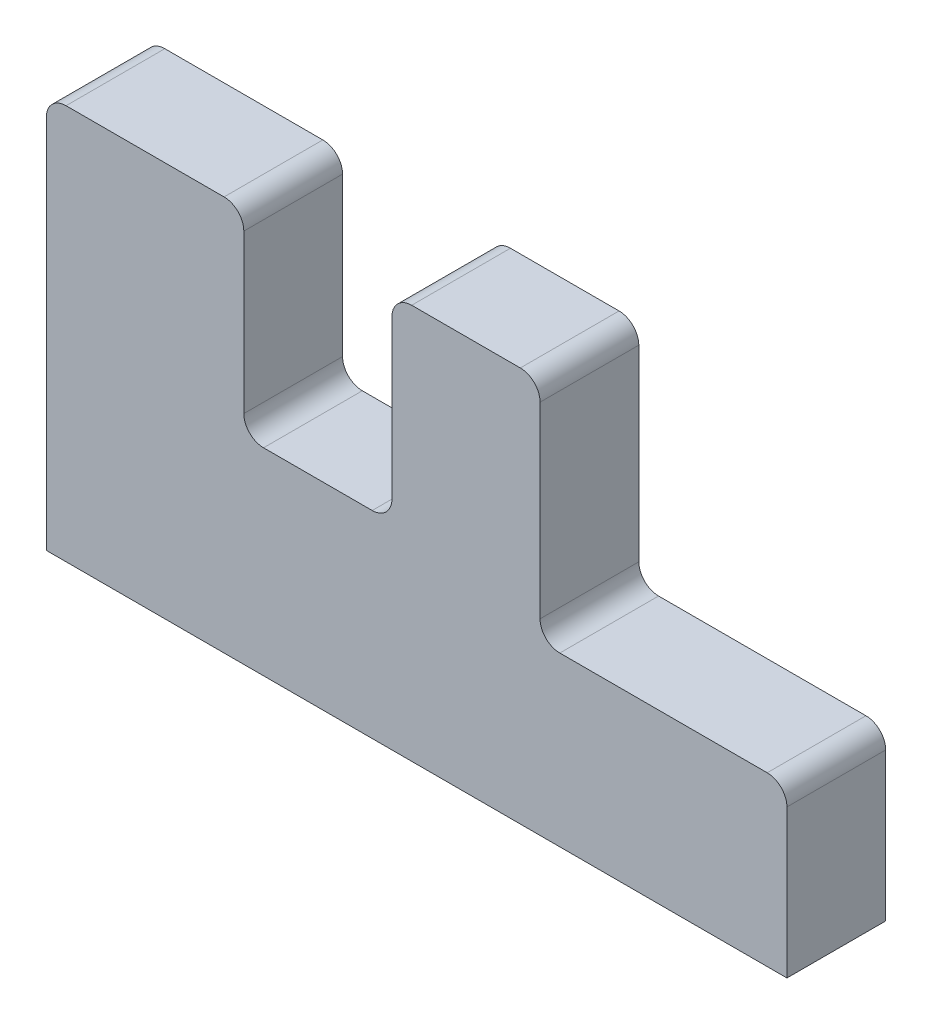
SolidWorks part; units mm, degrees
ref_plane "Front Plane" through (0, 0, 0) normal (0, 0, 1) x (1, 0, 0)
ref_plane "Top Plane" through (0, 0, 0) normal (0, 1, 0) x (1, 0, 0)
ref_plane "Right Plane" through (0, 0, 0) normal (1, 0, 0) x (0, 0, -1)
sketch "Sketch1" plane through (0, 0, 0) normal (0, 0, 1) x (1, 0, 0)
  line L0 (0, 0) -> (0, 50.8)
  line L1 (0, 50.8) -> (25.4, 50.8)
  line L2 (25.4, 50.8) -> (25.4, 25.4)
  line L3 (25.4, 25.4) -> (44.45, 25.4)
  line L4 (44.45, 25.4) -> (44.45, 50.8)
  line L5 (44.45, 50.8) -> (63.5, 50.8)
  line L6 (63.5, 50.8) -> (63.5, 21.59)
  line L7 (63.5, 21.59) -> (95.25, 21.59)
  line L8 (95.25, 21.59) -> (95.25, 0)
  line L9 (95.25, 0) -> (0, 0)
  point P13 (-55.7169, 45.0924)
  dimension "D1" = 95.25
  dimension "D2" = 50.8
  dimension "D3" = 25.4
  dimension "D4" = 44.45
  dimension "D5" = 63.5
  dimension "D6" = 21.59
  dimension "D7" = 25.4
extrude "Boss-Extrude1" add sketch "Sketch1" along normal blind 12.7
fillet "Fillet1" radius 2.54 8 edges at (0, 50.8, 6.35) (25.4, 50.8, 6.35) (25.4, 25.4, 6.35) (44.45, 25.4, 6.35) (44.45, 50.8, 6.35) (95.25, 21.59, 6.35) (63.5, 21.59, 6.35) (63.5, 50.8, 6.35)
